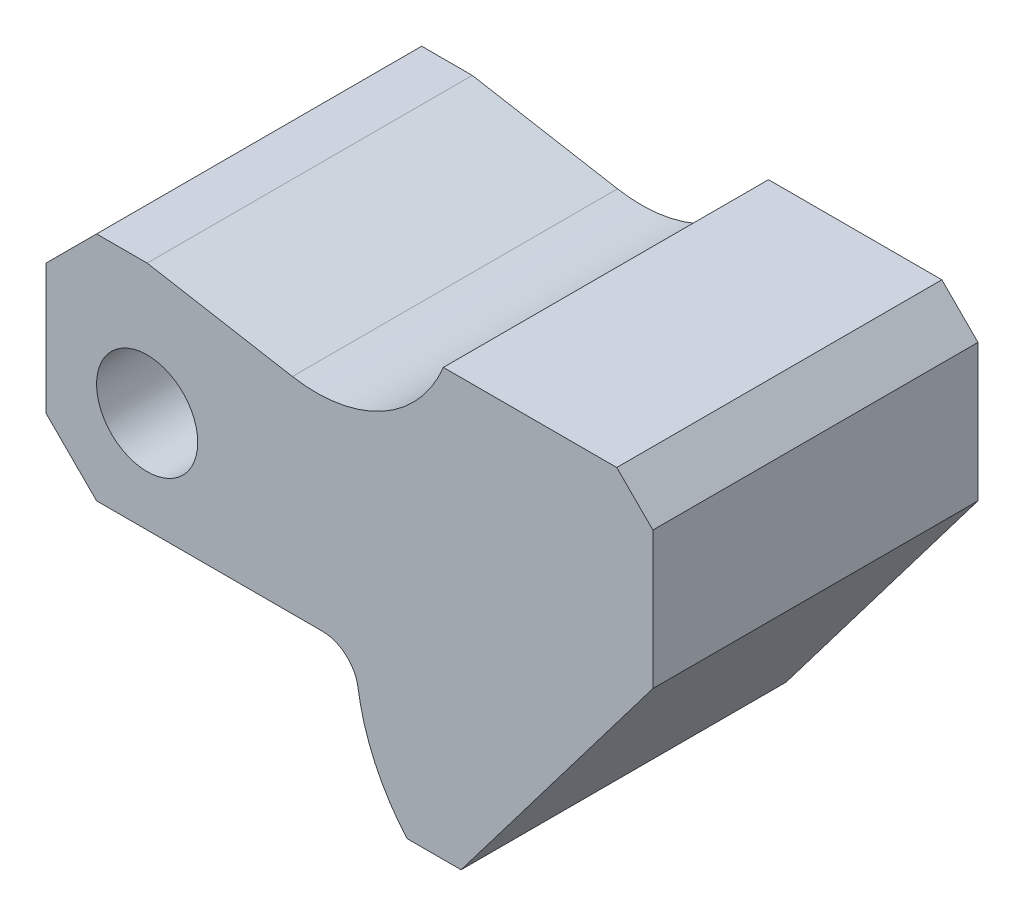
SolidWorks part; units mm, degrees
material "AISI 1020"
ref_plane "Front Plane" through (0, 0, 0) normal (0, 0, 1) x (1, 0, 0)
ref_plane "Top Plane" through (0, 0, 0) normal (0, 1, 0) x (1, 0, 0)
ref_plane "Right Plane" through (0, 0, 0) normal (1, 0, 0) x (0, 0, -1)
sketch "Sketch1" plane through (0, 0, 0) normal (0, 0, 1) x (1, 0, 0)
  line L0 (0, -32) -> (84, -32) construction
  line L1 (0, 0) -> (14, 0)
  line L2 (0, 0) -> (0, -32)
  line L3 (0, -32) -> (14, -32)
  line L4 (14, 0) -> (14, -32)
  line L5 (84, -32) -> (84, 8) construction
  line L6 (86.4516, -51) -> (57.4516, -51) construction
  line L7 (55, 8) -> (84, 8)
  line L8 (55, 8) -> (55, -16)
  line L9 (55, -16) -> (84, -16)
  line L10 (84, 8) -> (84, -16)
  line L11 (14, -32) -> (14, -51) construction
  line L12 (14, -51) -> (86.4516, -51) construction
  line L13 (86.4516, -51) -> (57.4516, -51) construction
  line L14 (84, -16) -> (57.4516, -51)
  line L15 (14, -32) -> (42.8636, -32)
  line L16 (14, 0) -> (34.104, -3.5449)
  line L17 (49.9547, -51) -> (57.4516, -51)
  line L18 (14, -32) -> (42.8636, -32)
  line L19 (14, -32) -> (14, -18) construction
  arc A0 (42.8636, -32) -> (49.9547, -51) centre (71.8636, -32) ccw
  circle A1 centre (14, -18) radius 7
  arc A2 (34.104, -3.5449) -> (55, 8) centre (37.4034, 15.1665) ccw
  point P18 (-24.6795, -34.913)
  dimension "D7" = 40
  dimension "D8" = 19
  dimension "D4" = 84
  dimension "D10" = 43.9297
  dimension "D12" = 29
  dimension "D13" = 14
  dimension "D14" = 14
  dimension "D3" = 19
  dimension "D1" = 14
  dimension "D2" = 32
  dimension "D5" = 29
  dimension "D6" = 24
  dimension "D9" = 29
  dimension "D11" = 190
  dimension "D15" = 59
extrude "Boss-Extrude1" add sketch "Sketch1" along normal blind 45 contours A2 L16 L4 L15 A0 L17 L14 L9 L8 | L4 L1 L2 L3 | L10 L7 L8 L9
chamfer "Chamfer1" distance 7 angle 45 1 edges at (0, 0, 22.5)
chamfer "Chamfer2" distance 7 angle 45 1 edges at (0, -32, 22.5)
chamfer "Chamfer3" distance 5 angle 45 1 edges at (84, 8, 22.5)
fillet "Fillet1" radius 5 1 edges at (42.8636, -32, 22.5)
